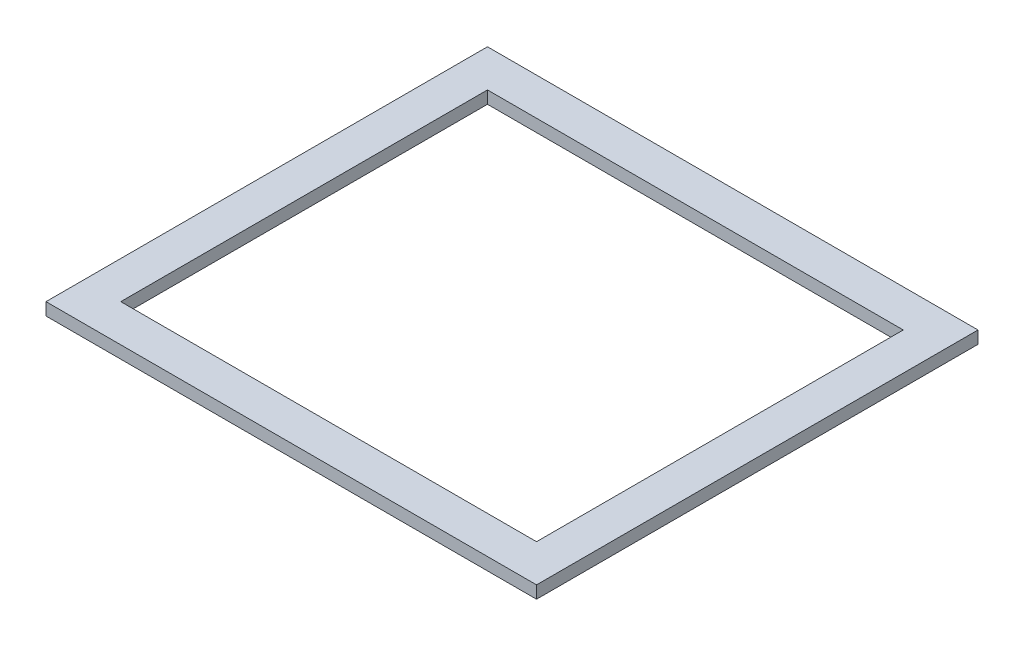
SolidWorks part; units mm, degrees
ref_plane "Alzado" through (0, 0, 0) normal (0, 0, 1) x (1, 0, 0)
ref_plane "Planta" through (0, 0, 0) normal (0, 1, 0) x (1, 0, 0)
ref_plane "Vista lateral" through (0, 0, 0) normal (1, 0, 0) x (0, 0, -1)
sketch "Croquis1" plane through (0, 0, 0) normal (0, 1, 0) x (1, 0, 0)
  line L0 (76.2, -76.2) -> (923.8, -76.2)
  line L1 (0, 0) -> (1000, 0)
  line L2 (0, 0) -> (0, -900)
  line L3 (0, -900) -> (1000, -900)
  line L4 (1000, 0) -> (1000, -900)
  line L5 (923.8, -76.2) -> (923.8, -823.8)
  line L6 (76.2, -823.8) -> (923.8, -823.8)
  line L7 (76.2, -76.2) -> (76.2, -823.8)
  dimension "D1" = 1000
  dimension "D2" = 900
  dimension "D3" = 76.2
extrude "Saliente-Extruir1" add sketch "Croquis1" along normal blind 25.4
